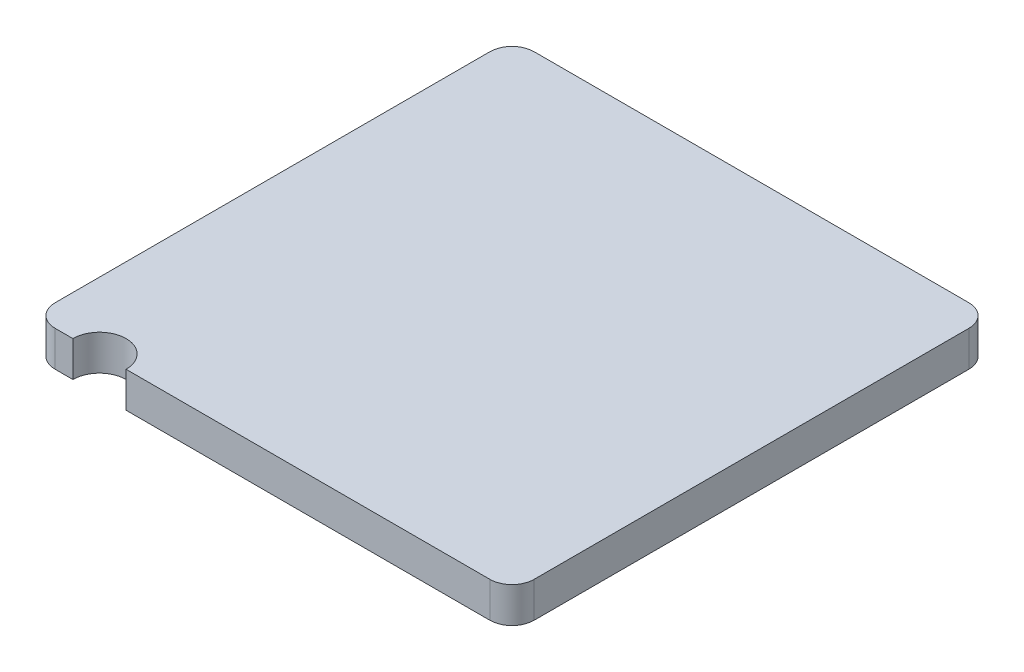
SolidWorks part; units mm, degrees
ref_plane "Front Plane" through (0, 0, 0) normal (0, 0, 1) x (1, 0, 0)
ref_plane "Top Plane" through (0, 0, 0) normal (0, 1, 0) x (1, 0, 0)
ref_plane "Right Plane" through (0, 0, 0) normal (1, 0, 0) x (0, 0, -1)
sketch "Sketch1" plane through (0, 0, 0) normal (0, 1, 0) x (1, 0, 0)
  line L1 (-1.35, -1.35) -> (1.35, -1.35)
  line L2 (-1.35, -1.35) -> (-1.35, 1.35)
  line L3 (-1.35, 1.35) -> (1.35, 1.35)
  line L4 (1.35, -1.35) -> (1.35, 1.35)
  line L5 (-1.35, -1.35) -> (1.35, 1.35) construction
  line L6 (-1.35, 1.35) -> (1.35, -1.35) construction
  point P0 (0, 0)
  dimension "D1" = 2.7
extrude "Boss-Extrude1" add sketch "Sketch1" along normal blind 0.2
fillet "Fillet1" radius 0.125 4 edges at (-1.35, 0.1, -1.35) (1.35, 0.1, -1.35) (1.35, 0.1, 1.35) (-1.35, 0.1, 1.35)
sketch "Sketch3" plane through (0, 0, 0) normal (0, -1, 0) x (1, 0, 0)
  line L0 (-1.225, 1.35) -> (1.225, 1.35) construction
  line L1 (-1.125, 1.35) -> (-0.825, 1.35)
  line L2 (0, -0.11) -> (0, 0.11) construction
  arc A0 (-1.125, 1.35) -> (-0.825, 1.35) centre (-0.975, 1.35) ccw
  dimension "D1" = 0.15
  dimension "D2" = 0.975
extrude "Cut-Extrude2" cut sketch "Sketch3" against normal through all
